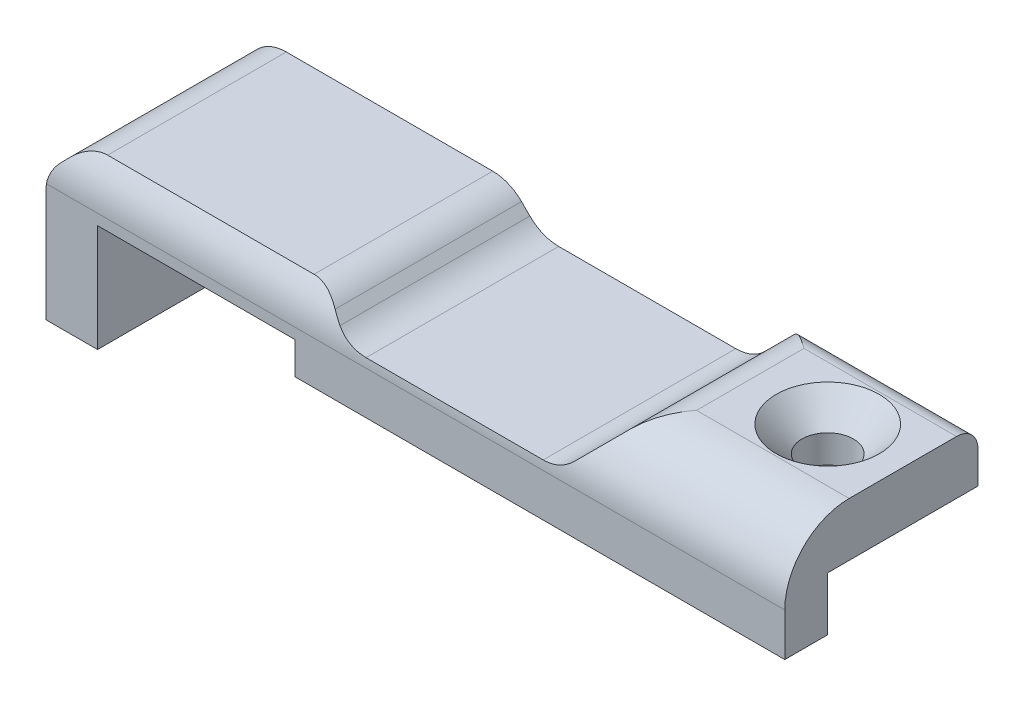
SolidWorks part; units mm, degrees
ref_plane "Front Plane" through (0, 0, 0) normal (0, 0, 1) x (1, 0, 0)
ref_plane "Top Plane" through (0, 0, 0) normal (0, 1, 0) x (1, 0, 0)
ref_plane "Right Plane" through (0, 0, 0) normal (1, 0, 0) x (0, 0, -1)
sketch "Sketch1" plane through (0, 0, 0) normal (0, 0, 1) x (1, 0, 0)
  line L0 (-20.079, 0) -> (-20.079, 1.905)
  line L1 (-20.079, 1.905) -> (-31.763, 1.905)
  line L2 (-31.763, 1.905) -> (-31.763, -4.445)
  line L3 (-31.763, -4.445) -> (-34.811, -4.445)
  line L4 (-34.811, -4.445) -> (-34.811, 2.1685)
  line L5 (-32.0265, 4.953) -> (-19.8172, 4.953)
  line L6 (8.89, 6.35) -> (8.89, 3.175)
  line L7 (0, 0) -> (-20.079, 0)
  line L9 (0, 3.175) -> (0, 0)
  line L10 (-1.842, 5.6436) -> (-3.7311, 3.7544)
  line L11 (-5.4366, 3.048) -> (-15.914, 3.048)
  line L12 (-17.6195, 3.7544) -> (-18.1116, 4.2466)
  line L13 (-0.1365, 6.35) -> (8.89, 6.35)
  line L14 (-34.1046, 3.874) -> (-33.732, 4.2466)
  line L15 (0, 3.175) -> (8.89, 3.175)
  arc A0 (-0.1365, 6.35) -> (-1.842, 5.6436) centre (-0.1365, 3.938) ccw
  arc A1 (-3.7311, 3.7544) -> (-5.4366, 3.048) centre (-5.4366, 5.46) cw
  arc A2 (-15.914, 3.048) -> (-17.6195, 3.7544) centre (-15.914, 5.46) cw
  arc A3 (-18.1116, 4.2466) -> (-19.8172, 4.953) centre (-19.8172, 2.541) ccw
  arc A4 (-32.0265, 4.953) -> (-33.732, 4.2466) centre (-32.0265, 2.541) ccw
  arc A5 (-34.1046, 3.874) -> (-34.811, 2.1685) centre (-32.399, 2.1685) ccw
  point P0 (0, 0)
  point P4 (0, 0)
  point P10 (-17.8656, 4.0005)
  point P19 (0, 0)
  point P20 (-29.5922, 5.588)
  point P21 (0, 0)
  dimension "D16" = 2.412
  dimension "D17" = 2.412
  dimension "D1" = 11.684
  dimension "D2" = 1.905
  dimension "D3" = 3.048
  dimension "D4" = 3.048
  dimension "D5" = 3.048
  dimension "D6" = 45
  dimension "D7" = 3.048
  dimension "D9" = 8.89
  dimension "D11" = 6.35
  dimension "D13" = 3.048
  dimension "D14" = 45
  dimension "D10" = 3.175
  dimension "D15" = 3.175
  dimension "D8" = 28.969
  dimension "D12" = 3.048
extrude "Boss-Extrude1" add sketch "Sketch1" along normal blind 11.43
sketch "Sketch2" plane through (0, 0, 11.43) normal (0, 0, 1) x (1, 0, 0)
  line L1 (0, 0) -> (8.89, 0)
  line L2 (0, 0) -> (0, 3.175)
  line L3 (0, 3.175) -> (8.89, 3.175)
  line L4 (8.89, 0) -> (8.89, 3.175)
  line L5 (0, 0) -> (8.89, 3.175) construction
  line L6 (0, 3.175) -> (8.89, 0) construction
  point P4 (4.445, 1.5875)
extrude "Boss-Extrude2" add sketch "Sketch2" against normal blind 2.54
sketch "Sketch3" plane through (0, 6.35, 0) normal (0, 1, 0) x (1, 0, 0)
  line L1 (0, 0) -> (8.89, 0)
  line L2 (0, 0) -> (0, -8.89)
  line L3 (0, -8.89) -> (8.89, -8.89)
  line L4 (8.89, -8.89) -> (8.89, 0)
  line L5 (0, -8.89) -> (8.89, -8.89)
  line L6 (0, 0) -> (0, -8.89)
  line L7 (8.89, 0) -> (0, 0)
  line L8 (8.89, -8.89) -> (8.89, 0)
  line L9 (0, -8.89) -> (8.89, -8.89)
  line L10 (0, 0) -> (0, -8.89)
  line L11 (8.89, 0) -> (0, 0)
  line L12 (8.89, 0) -> (8.89, -8.89)
  line L13 (0, 0) -> (8.89, -8.89) construction
  line L14 (0, -8.89) -> (8.89, 0) construction
  circle A0 centre (4.445, -4.445) radius 1.524
  point P4 (4.445, -4.445)
  dimension "D2" = 3.048
  dimension "D1" = 0
extrude "Cut-Extrude1" cut sketch "Sketch3" against normal through all contours A0
sketch "Sketch4" plane through (8.89, 0, 0) normal (1, 0, 0) x (0, 0, -1)
  line L0 (-11.43, 2.54) -> (-11.43, 3.175)
  line L1 (-11.43, 0) -> (-11.43, 6.35) construction
  line L2 (-11.43, 2.54) -> (-11.43, 6.35)
  line L4 (-1.27, 6.35) -> (-5.969, 6.35)
  line L5 (0, 5.08) -> (0, 3.916)
  line L6 (0, 3.175) -> (0, 6.35) construction
  line L7 (-2.921, 6.35) -> (-5.969, 6.35) construction
  line L8 (-2.921, 6.35) -> (-5.969, 6.35)
  line L9 (-1.27, 6.35) -> (0, 6.35)
  line L10 (0, 6.35) -> (0, 5.08)
  line L11 (-11.43, 6.35) -> (-7.62, 6.35)
  line L12 (-11.43, 6.35) -> (0, 6.35) construction
  arc A0 (-7.62, 6.35) -> (-11.43, 2.54) centre (-7.62, 2.54) ccw
  arc A1 (0, 5.08) -> (-1.27, 6.35) centre (-1.27, 5.08) ccw
  point P10 (-11.43, 6.35)
  point P19 (0, 6.35)
  point P22 (0, 0)
  line M2 (0, 3.175) -> (0, 6.35)
  line M3 (0, 6.35) -> (-11.43, 6.35)
  line M4 (-11.43, 6.35) -> (-11.43, 0)
  dimension "D2" = 1.27
  dimension "D1" = 1.651
  dimension "D3" = 1.651
extrude "Cut-Extrude2" cut sketch "Sketch4" against normal through all and the other way through all contours A0 M3 M4 | A1 M2 M3
chamfer "Chamfer1" distance 1.524 angle 45 1 edges at (4.445, 6.35, 5.969)
equation "\"D4@Sketch1\"=\"D3@Sketch1\""
equation "\"D5@Sketch1\"=\"D3@Sketch1\""
equation "\"D7@Sketch1\"=\"D5@Sketch1\""
equation "\"D13@Sketch1\"=\"D4@Sketch1\""
equation "\"D1@Sketch4\"=\"D3@Sketch4\""
